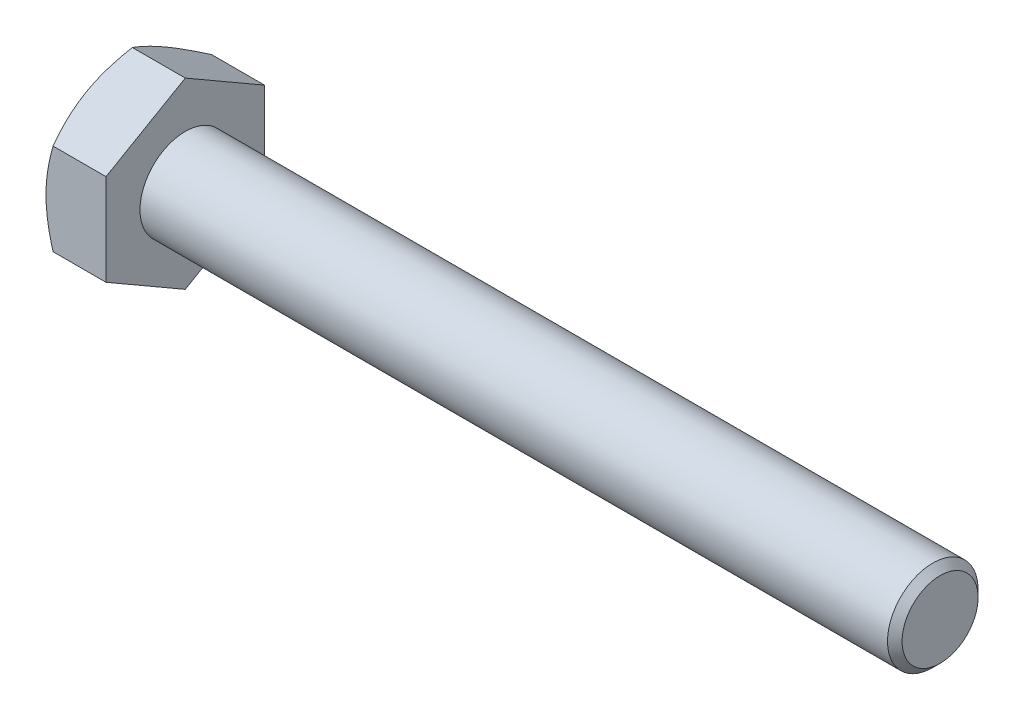
SolidWorks part; units mm, degrees
ref_plane "Plane1" through (0, 0, 0) normal (0, 0, 1) x (1, 0, 0)
ref_plane "Plane2" through (0, 0, 0) normal (0, 1, 0) x (1, 0, 0)
ref_plane "Plane3" through (0, 0, 0) normal (1, 0, 0) x (0, 0, -1)
sketch "Sketch1" plane through (0, 0, 0) normal (1, 0, 0) x (0, 0, -1)
  line L0 (10.5, 6.0622) -> (10.5, -6.0622)
  line L1 (-10.5, 6.0622) -> (-10.5, -6.0622)
  line L2 (10.5, -6.0622) -> (0, -12.1244)
  line L3 (0, -12.1244) -> (-10.5, -6.0622)
  line L4 (10.5, 6.0622) -> (0, 12.1244)
  line L5 (0, 12.1244) -> (-10.5, 6.0622)
  dimension "Width_flats" = 21
  dimension "D2" = 120
  dimension "D3" = 10.5
  dimension "D4" = 10.5
  dimension "D5" = 10.5
extrude "BaseHead" add sketch "Sketch1" along normal blind 7.95
sketch "BodySke" plane through (0, 0, 0) normal (0, 0, 1) x (1, 0, 0)
  line L0 (0, 6.0622) -> (0, -6.0622) construction
  line L1 (0, 0) -> (107.95, 0)
  line L2 (0, 0) -> (0, 6)
  line L3 (0, 6) -> (106.986, 6)
  line L4 (107.95, 0) -> (107.95, 5.036)
  line L5 (7.95, 12.1244) -> (7.95, 6.0622) construction
  line L6 (107.95, 5.036) -> (106.986, 6)
  line L7 (0, 0) -> (96.52, 0) construction
  line L8 (107.95, -5.036) -> (106.986, -6) construction
  line L9 (0, -6) -> (106.986, -6) construction
  line L10 (9.7, 15.24) -> (9.7, -1.27) construction
  line L11 (7.95, 15.24) -> (7.95, -1.27) construction
  line L12 (7.95, 6.0622) -> (7.95, -6.0622) construction
  dimension "Length" = 100
  dimension "Body_ch_ang" = 45
  dimension "Diameter" = 12
  dimension "Minor_dia" = 10.072
  dimension "Advance" = 1.75
  dimension "Thread_nom" = 100
revolve "BaseBody" add sketch "BodySke"
cosmetic thread "ThreadCosmetic"
fillet "HeadFillet" [suppressed] radius 0.6
sketch "Sketch3" plane through (0, 0, 0) normal (0, 0, 1) x (1, 0, 0)
  line L0 (0, 10.5) -> (3.8246, 17.1244)
  line L1 (0, 12.1244) -> (0, 6.0622) construction
  line L2 (3.8246, 17.1244) -> (3.8246, 22.1244)
  line L3 (3.8246, 22.1244) -> (-10, 22.1244)
  line L4 (-10, 22.1244) -> (-10, 10.5)
  line L5 (-10, 10.5) -> (0, 10.5)
  line L6 (0, 0) -> (99.06, 0) construction
  line L7 (7.95, 12.1244) -> (0, 12.1244) construction
  dimension "D1" = 10.5
  dimension "D2" = 5
  dimension "D3" = 10
  dimension "D4" = 5
  dimension "Head_ch_ang" = 30
revolve "HeadChamfer" cut sketch "Sketch3" angle 360 about L6
sketch "ThdSchSke" plane through (0, 0, 0) normal (0, 0, 1) x (1, 0, 0)
  line L0 (9.7, -5.036) -> (9.025, -6)
  line L1 (9.7, -5.036) -> (10.375, -6)
  line L2 (10.375, -6) -> (10.375, -7.5)
  line L3 (-3.175, 0) -> (5.1513, 0) construction
  line L5 (10.375, -7.5) -> (9.025, -7.5)
  line L6 (9.025, -7.5) -> (9.025, -6)
  dimension "Thread_minor" = 10.072
  dimension "Diameter" = 12
  dimension "Start" = 9.7
  dimension "SideAngle" = 55
  dimension "VeeAngle" = 70
  dimension "Overcut" = 15
revolve "ThreadSchematic" [suppressed] cut sketch "ThdSchSke" angle 360 about L3
pattern_linear "ThdSchPat" [suppressed]
equation "\"D3@Sketch1\" = \"Width_flats@Sketch1\" / 2"
equation "\"D4@Sketch1\" = \"D3@Sketch1\""
equation "\"D5@Sketch1\" = \"D4@Sketch1\""
equation "\"Thread_minor@ThreadCosmetic\" = \"Minor_dia@BodySke\""
equation "\"D1@Sketch3\" = \"Width_flats@Sketch1\" / 2"
equation "' \"D1@Sketch4\" = \"Width_flats@Sketch1\""
equation "\"Thread_length@ThreadCosmetic\" = ((sgn( (\"Length@BodySke\" - \"Advance@BodySke\" ) - \"Thread_nom@BodySke\" )-1)*( (\"Length@BodySke\" - \"Advance@BodySke\" ) - \"Thread_nom@BodySke\" ))/-2+ \"Thread_nom@BodySke\""
equation "\"Thread_minor@ThdSchSke\" = \"Minor_dia@BodySke\""
equation "\"Diameter@ThdSchSke\" = \"Diameter@BodySke\""
equation "\"Overcut@ThdSchSke\" = \"Diameter@BodySke\" * 1.25"
equation "\"Start@ThdSchSke\" = \"Head_ht@BaseHead\" + \"Length@BodySke\" - \"Thread_length@ThreadCosmetic\"  '---Non-countersunk---"
equation "\"Num_threads@ThdSchPat\" = int( \"Thread_length@ThreadCosmetic\" / \"Advance@BodySke\" + 0.999 )  + 1"
equation "\"Advance@ThdSchPat\" = \"Thread_length@ThreadCosmetic\" /  (\"Num_threads@ThdSchPat\" - 1) 'relax it"
equation "\"Num_threads@ThdSchPat\" = \"Num_threads@ThdSchPat\" - sgn( \"Num_threads@ThdSchPat\" - 1) '---chamfered tips only---"
